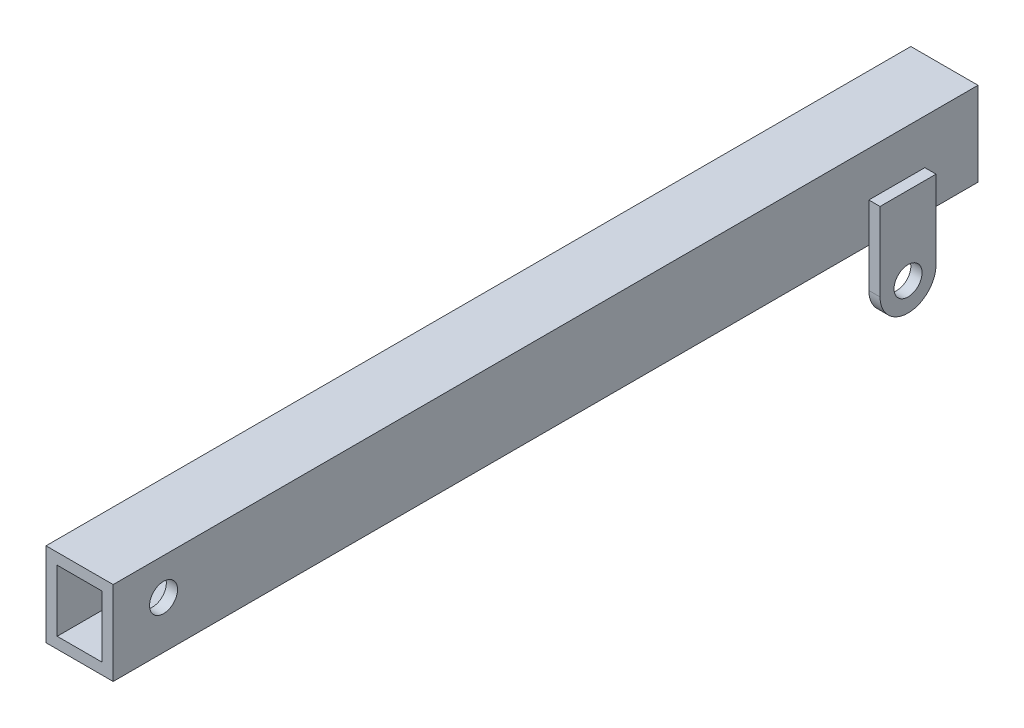
SolidWorks part; units mm, degrees
ref_plane "Alzado" through (0, 0, 0) normal (0, 0, 1) x (1, 0, 0)
ref_plane "Planta" through (0, 0, 0) normal (0, 1, 0) x (1, 0, 0)
ref_plane "Vista lateral" through (0, 0, 0) normal (1, 0, 0) x (0, 0, -1)
sketch "Croquis1" plane through (0, 0, 0) normal (0, 0, 1) x (1, 0, 0)
  line L1 (-6, -7.5) -> (6, -7.5)
  line L2 (-6, -7.5) -> (-6, 7.5)
  line L3 (-6, 7.5) -> (6, 7.5)
  line L4 (6, -7.5) -> (6, 7.5)
  line L5 (-6, -7.5) -> (6, 7.5) construction
  line L6 (-6, 7.5) -> (6, -7.5) construction
  line L7 (-4, -5.5) -> (4, -5.5)
  line L8 (-4, -5.5) -> (-4, 5.5)
  line L9 (-4, 5.5) -> (4, 5.5)
  line L10 (4, -5.5) -> (4, 5.5)
  line L11 (-4, -5.5) -> (4, 5.5) construction
  line L12 (-4, 5.5) -> (4, -5.5) construction
  point P0 (0, 0)
  point P6 (0, 0)
  dimension "D1" = 12
  dimension "D2" = 15
  dimension "D3" = 2
  dimension "D4" = 2
extrude "Saliente-Extruir1" add sketch "Croquis1" along normal mid plane 319
sketch "Croquis2" plane through (6, 0, 0) normal (1, 0, 0) x (0, 0, -1)
  line L0 (-159.5, -7.5) -> (159.5, -7.5) construction
  line L2 (-145, -14.5) -> (-145, -0.5)
  line L3 (-145, -0.5) -> (-135, -0.5)
  line L4 (-135, -14.5) -> (-135, -0.5)
  line L5 (-145, -14.5) -> (-135, -0.5) construction
  line L6 (-145, -0.5) -> (-135, -14.5) construction
  arc A0 (-145, -14.5) -> (-135, -14.5) centre (-140, -14.5) ccw
  circle A1 centre (-140, -14.5) radius 2.5
  point P0 (-140, -7.5)
  dimension "D3" = 5
  dimension "D6" = 5
  dimension "D1" = 14
  dimension "D2" = 10
  dimension "D4" = 135
  dimension "D5" = 7
extrude "Saliente-Extruir2" add sketch "Croquis2" along normal blind 2
mirror "Simetría1" about plane through (0, 0, 0) normal (1, 0, 0) of "Saliente-Extruir2"
mirror "Simetría2" about plane through (0, 0, 0) normal (0, 0, 1) of "Simetría1", "Saliente-Extruir2"
sketch "Sketch1" plane through (6, 0, 0) normal (1, 0, 0) x (0, 0, -1)
  line L1 (-159.5, 7.5) -> (0, 7.5)
  line L2 (-159.5, 7.5) -> (-159.5, -26.8057)
  line L3 (-159.5, -26.8057) -> (0, -26.8057)
  line L4 (0, 7.5) -> (0, -26.8057)
extrude "Cut-Extrude1" cut sketch "Sketch1" against normal through all both and the other way through all
sketch "Sketch2" plane through (6, 0, 0) normal (1, 0, 0) x (0, 0, -1)
  line L0 (0, -7.5) -> (135, -7.5) construction
  line L1 (0, 7.5) -> (12, 7.5)
  line L2 (0, 7.5) -> (0, -7.5)
  line L3 (0, -7.5) -> (12, -7.5)
  line L4 (12, 7.5) -> (12, -7.5) construction
  circle A0 centre (7, 0) radius 2.5
  dimension "D2" = 5
  dimension "D1" = 12
  dimension "D3" = 5
  dimension "D4" = 7.5
sketch "Sketch4" plane through (-6, 0, 0) normal (-1, 0, 0) x (0, 0, 1)
  line L0 (0, -7.5) -> (-135, -7.5) construction
  line L1 (0, 7.5) -> (-16.5674, 7.5)
  line L2 (0, 7.5) -> (0, -7.5)
  line L3 (0, -7.5) -> (-16.5674, -7.5)
  line L4 (-16.5674, 7.5) -> (-16.5674, -7.5)
  circle A0 centre (-11, 1) radius 2.5
  dimension "D1" = 5
  dimension "D2" = 11
  dimension "D3" = 6.5
sketch "Sketch5" plane through (-6, 0, 0) normal (-1, 0, 0) x (0, 0, 1)
  circle A0 centre (-9, 1) radius 2.5
extrude "Cut-Extrude2" cut sketch "Sketch5" against normal through all
sketch "Sketch6" plane through (-6, 0, 0) normal (-1, 0, 0) x (0, 0, 1)
  line L0 (-145, -7.5) -> (-159.5, -7.5) construction
  line L1 (-159.5, 7.5) -> (-154.5, 7.5)
  line L2 (-159.5, 7.5) -> (-159.5, -7.5)
  line L3 (-159.5, -7.5) -> (-154.5, -7.5)
  line L4 (-154.5, 7.5) -> (-154.5, -7.5)
  dimension "D1" = 5
extrude "Cut-Extrude3" cut sketch "Sketch6" against normal through all both and the other way through all
